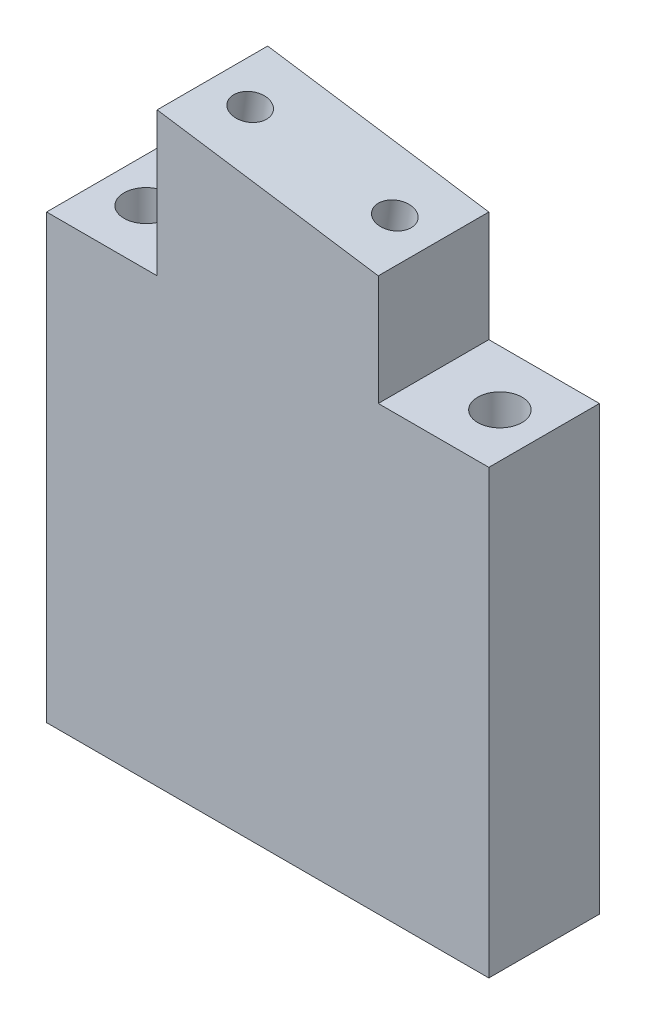
SolidWorks part; units mm, degrees
ref_plane "Plan de face" through (0, 0, 0) normal (0, 0, 1) x (1, 0, 0)
ref_plane "Plan de dessus" through (0, 0, 0) normal (0, 1, 0) x (1, 0, 0)
ref_plane "Plan de droite" through (0, 0, 0) normal (1, 0, 0) x (0, 0, -1)
sketch "Esquisse1" plane through (0, 0, 0) normal (0, 0, 1) x (1, 0, 0)
  line L0 (-13.3477, 16.3953) -> (-3.3477, 16.3953)
  line L1 (16.6523, 16.3953) -> (26.6523, 16.3953)
  line L2 (-13.3477, 16.3953) -> (-13.3477, -23.6047)
  line L3 (-13.3477, -23.6047) -> (26.6523, -23.6047)
  line L4 (26.6523, 16.3953) -> (26.6523, -23.6047)
  line L5 (-3.3477, 26.3953) -> (-3.3477, 29.3953)
  line L6 (-3.3477, 16.3953) -> (-3.3477, 26.3953)
  line L7 (-3.3477, 29.3953) -> (16.6523, 26.3953)
  line L8 (16.6523, 16.3953) -> (16.6523, 26.3953)
  dimension "D1" = 40
  dimension "D2" = 10
  dimension "D3" = 40
  dimension "D4" = 20
  dimension "D5" = 10
  dimension "D6" = 3
extrude "Boss.-Extru.1" add sketch "Esquisse1" along normal blind 10
sketch "Esquisse2" plane through (0, 16.3953, 0) normal (0, 1, 0) x (1, 0, 0)
  line L0 (-3.3477, -10) -> (-3.3477, 0) construction
  line L1 (-3.3477, 0) -> (-13.3477, 0) construction
  line L3 (16.6523, -10) -> (16.6523, 0) construction
  line L4 (26.6523, 0) -> (16.6523, 0) construction
  circle A0 centre (22.6523, -5) radius 2
  circle A1 centre (-9.3477, -5) radius 2
  point P8 (-3.3477, -5)
  dimension "D1" = 4
  dimension "D2" = 5
  dimension "D3" = 5
  dimension "D4" = 4
  dimension "D5" = 6
  dimension "D6" = 6
sketch "Esquisse4" plane through (4.2386, 28.2574, 0) normal (0.1483, 0.9889, 0) x (0.9889, -0.1483, 0)
  line L0 (-7.6712, -10) -> (-7.6712, 0) construction
  line L1 (12.5526, -10) -> (12.5526, 0) construction
  circle A0 centre (-4.1712, -5.0472) radius 1.5
  circle A1 centre (9.0526, -5.0472) radius 1.5
  point P4 (-7.6712, -5)
  point P7 (12.5526, -5)
  dimension "D1" = 3
  dimension "D2" = 3
  dimension "D3" = 3.5
  dimension "D4" = 3.5
extrude "Enlèv. mat.-Extru.3" cut sketch "Esquisse4" against normal blind 10
extrude "Enlèv. mat.-Extru.4" cut sketch "Esquisse2" against normal blind 50
